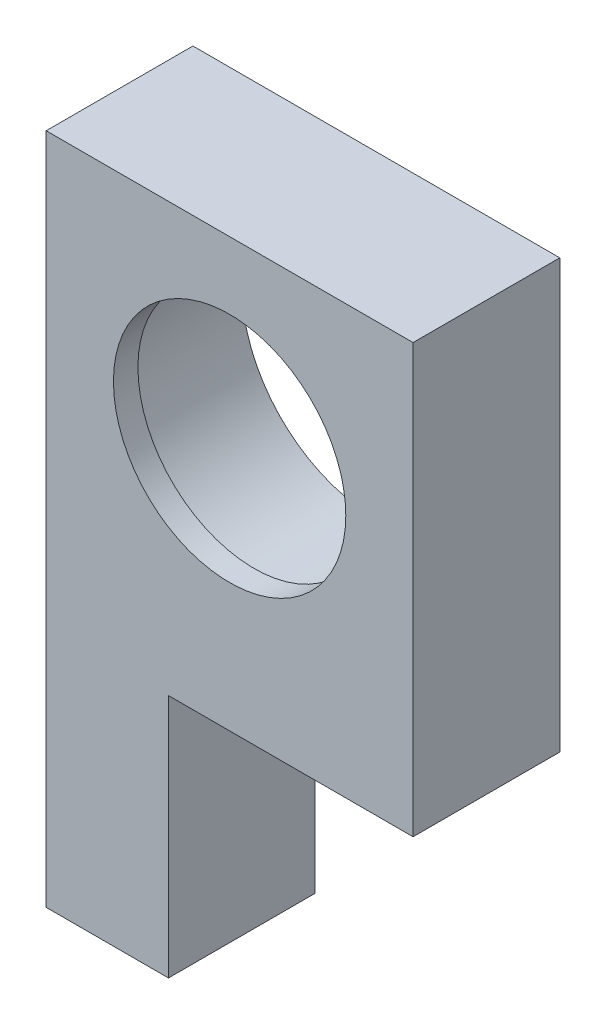
SolidWorks part; units mm, degrees
ref_plane "Ebene vorne" through (0, 0, 0) normal (0, 0, 1) x (1, 0, 0)
ref_plane "Ebene oben" through (0, 0, 0) normal (0, 1, 0) x (1, 0, 0)
ref_plane "Ebene rechts" through (0, 0, 0) normal (1, 0, 0) x (0, 0, -1)
sketch "Skizze1" plane through (0, 0, 0) normal (0, 0, 1) x (1, 0, 0)
  line L0 (15, 15) -> (-15, 15)
  line L1 (-15, 15) -> (-15, -40)
  line L2 (15, -20) -> (15, 15)
  line L3 (-15, -40) -> (-5, -40)
  line L4 (-5, -40) -> (-5, -20)
  line L5 (15, -20) -> (-5, -20)
  circle A0 centre (0, 0) radius 9.5
  dimension "D1" = 19
  dimension "D6" = 10
  dimension "D2" = 20
  dimension "D3" = 15
  dimension "D4" = 20
  dimension "D5" = 15
  dimension "D7" = 20
extrude "Aufsatz-Linear austragen2" add sketch "Skizze1" along normal blind 12
sketch "Skizze9" plane through (0, 0, 0) normal (0, 0, -1) x (-1, 0, 0)
  circle A0 centre (0, 0) radius 11
  dimension "D1" = 22
extrude "Schnitt-Linear austragen2" cut sketch "Skizze9" against normal blind 10
